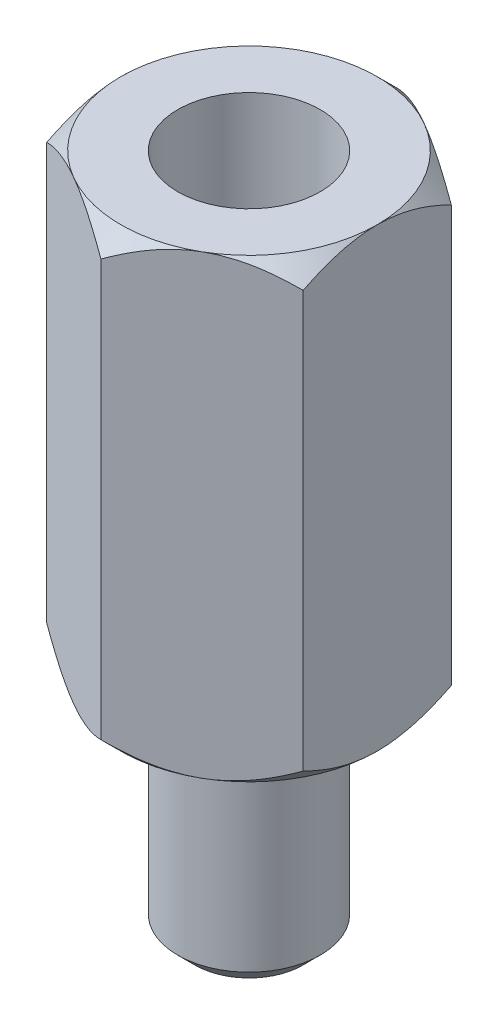
SolidWorks part; units mm, degrees
ref_plane "Front Plane" through (0, 0, 0) normal (0, 0, 1) x (1, 0, 0)
ref_plane "Top Plane" through (0, 0, 0) normal (0, 1, 0) x (1, 0, 0)
ref_plane "Right Plane" through (0, 0, 0) normal (1, 0, 0) x (0, 0, -1)
sketch "Sketch1" plane through (0, 0, 0) normal (0, 1, 0) x (1, 0, 0)
  circle A0 centre (0, 0) radius 1.25
  dimension "D1" = 2.5
extrude "Boss-Extrude1" add sketch "Sketch1" along normal blind 3.9
sketch "Sketch2" plane through (0, 3.9, 0) normal (0, 1, 0) x (1, 0, 0)
  line L1 (0, 2.5981) -> (-2.25, 1.299)
  line L2 (-2.25, 1.299) -> (-2.25, -1.299)
  line L3 (-2.25, -1.299) -> (0, -2.5981)
  line L4 (0, -2.5981) -> (2.25, -1.299)
  line L5 (2.25, -1.299) -> (2.25, 1.299)
  line L6 (2.25, 1.299) -> (0, 2.5981)
  circle A0 centre (0, 0) radius 2.25 construction
  dimension "D1" = 4.5
extrude "Boss-Extrude2" add sketch "Sketch2" along normal blind 8
sketch "Sketch3" plane through (0, 11.9, 0) normal (0, 1, 0) x (1, 0, 0)
  circle A0 centre (0, 0) radius 1.25
  dimension "D1" = 2.5
extrude "Cut-Extrude1" cut sketch "Sketch3" against normal blind 4.8
sketch "Sketch5" plane through (0, 11.9, 0) normal (0, 1, 0) x (1, 0, 0)
  circle A0 centre (0, 0) radius 2.25
extrude "Cut-Extrude2" cut sketch "Sketch5" against normal through all draft 45 flip side to cut
sketch "Sketch6" plane through (0, 3.9, 0) normal (0, -1, 0) x (1, 0, 0)
  circle A0 centre (0, 0) radius 2.25
extrude "Cut-Extrude3" cut sketch "Sketch6" against normal through all draft 45 flip side to cut
chamfer "Chamfer1" distance 0.3 angle 45 1 edges at (0, 0, 1.25)
